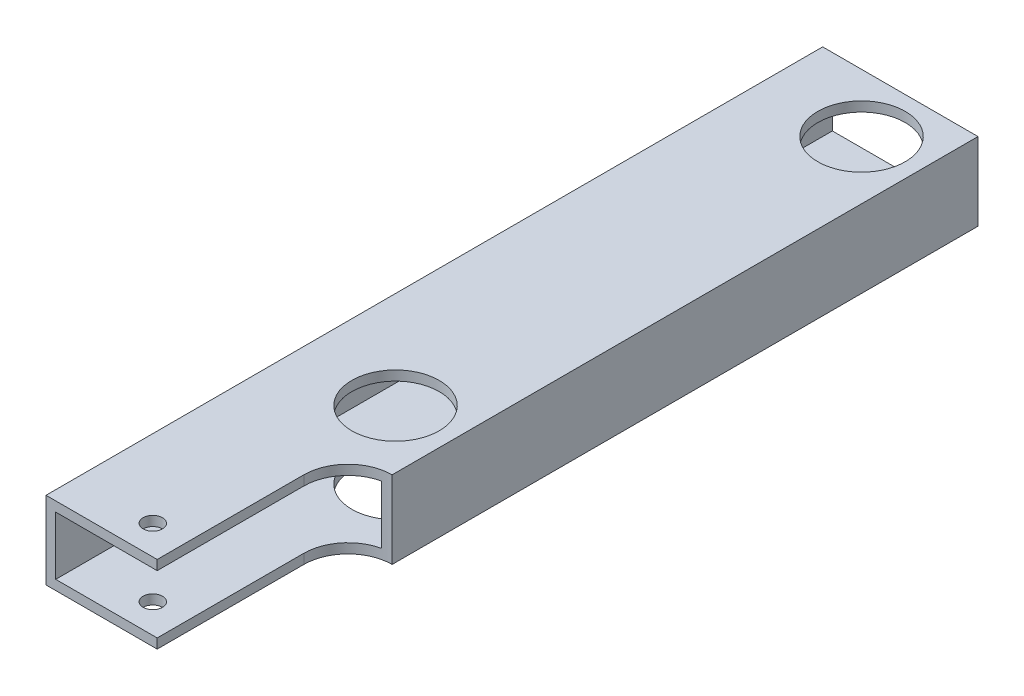
SolidWorks part; units mm, degrees
ref_plane "Front" through (0, 0, 0) normal (0, 0, 1) x (1, 0, 0)
ref_plane "Top" through (0, 0, 0) normal (0, 1, 0) x (1, 0, 0)
ref_plane "Right" through (0, 0, 0) normal (1, 0, 0) x (0, 0, -1)
sketch "Sketch1" plane through (0, 0, 0) normal (0, 0, 1) x (1, 0, 0)
  line L0 (3.175, 3.175) -> (47.625, 3.175)
  line L1 (0, 0) -> (50.8, 0)
  line L2 (0, 0) -> (0, 25.4)
  line L3 (0, 25.4) -> (50.8, 25.4)
  line L4 (50.8, 0) -> (50.8, 25.4)
  line L5 (47.625, 3.175) -> (47.625, 22.225)
  line L6 (3.175, 22.225) -> (47.625, 22.225)
  line L7 (3.175, 3.175) -> (3.175, 22.225)
  dimension "D1" = 25.4
  dimension "D2" = 50.8
  dimension "D3" = 3.175
extrude "Boss-Extrude1" add sketch "Sketch1" along normal blind 254
sketch "Sketch2" plane through (0, 25.4, 0) normal (0, 1, 0) x (1, 0, 0)
  line L0 (31.75, 0) -> (31.75, -19.05) construction
  line L2 (31.75, -19.05) -> (31.75, -171.45) construction
  line L4 (50.8, -254) -> (50.8, 0) construction
  line L5 (50.8, 0) -> (0, 0) construction
  circle A0 centre (31.75, -19.05) radius 14.2875
  circle A1 centre (31.75, -171.45) radius 14.2875
  dimension "D1" = 28.575
  dimension "D4" = 28.575
  dimension "D2" = 19.05
  dimension "D3" = 152.4
  dimension "D5" = 19.05
extrude "Cut-Extrude1" cut sketch "Sketch2" against normal through all
sketch "Sketch3" plane through (0, 25.4, 0) normal (0, 1, 0) x (1, 0, 0)
  line L0 (25.4, -244.475) -> (25.4, -254) construction
  line L1 (50.8, -254) -> (0, -254) construction
  circle A0 centre (25.4, -244.475) radius 3.175
  dimension "D1" = 6.35
  dimension "D2" = 9.525
extrude "Cut-Extrude2" cut sketch "Sketch3" against normal through all
sketch "Sketch4" plane through (0, 25.4, 0) normal (0, 1, 0) x (1, 0, 0)
  line L0 (36.3589, -254) -> (36.3589, -206.0354)
  line L1 (50.8, -254) -> (0, -254) construction
  line L2 (50.8, -191.5943) -> (50.8, -254)
  line L3 (50.8, -254) -> (50.8, 0) construction
  line L4 (50.8, -254) -> (36.3589, -254)
  arc A0 (50.8, -191.5943) -> (36.3589, -206.0354) centre (50.8, -206.0354) ccw
extrude "Cut-Extrude3" cut sketch "Sketch4" against normal through all
